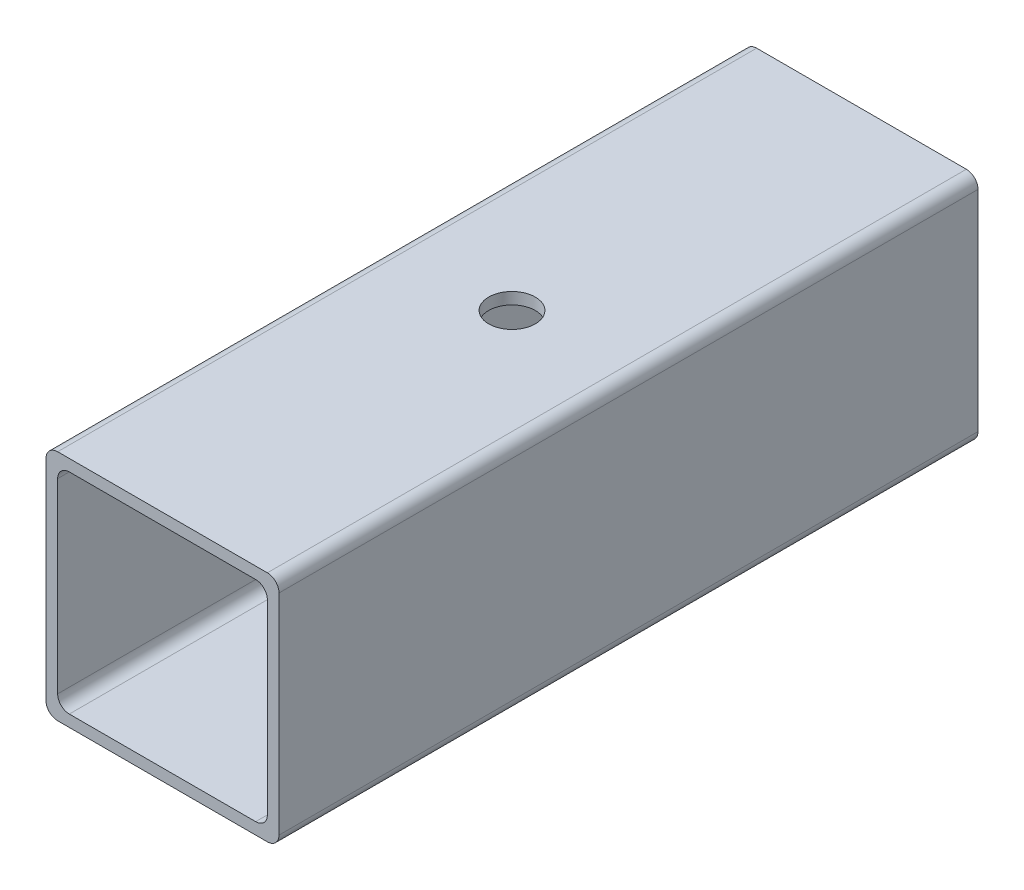
SolidWorks part; units mm, degrees
ref_plane "Płaszczyzna przednia" through (0, 0, 0) normal (0, 0, 1) x (1, 0, 0)
ref_plane "Płaszczyzna górna" through (0, 0, 0) normal (0, 1, 0) x (1, 0, 0)
ref_plane "Płaszczyzna prawa" through (0, 0, 0) normal (1, 0, 0) x (0, 0, -1)
sketch "Sketch1" plane through (0, 0, 0) normal (0, 0, 1) x (1, 0, 0)
  line L1 (-30, 30) -> (30, 30)
  line L2 (-30, 30) -> (-30, -30)
  line L3 (-30, -30) -> (30, -30)
  line L4 (30, 30) -> (30, -30)
  line L5 (-30, 30) -> (30, -30) construction
  line L6 (-30, -30) -> (30, 30) construction
  line L7 (-27, 27) -> (27, 27)
  line L8 (-27, 27) -> (-27, -27)
  line L9 (-27, -27) -> (27, -27)
  line L10 (27, 27) -> (27, -27)
  line L11 (-27, 27) -> (27, -27) construction
  line L12 (-27, -27) -> (27, 27) construction
  point P0 (0, 0)
  point P6 (0, 0)
  dimension "D1" = 60
  dimension "D2" = 60
  dimension "D3" = 54
  dimension "D4" = 54
extrude "Boss-Extrude1" add sketch "Sketch1" along normal blind 180
fillet "Fillet1" radius 3 8 edges at (-27, -27, 90) (27, -27, 90) (27, 27, 90) (-27, 27, 90) (30, -30, 90) (-30, -30, 90) (-30, 30, 90) (30, 30, 90)
sketch "Sketch2" plane through (0, 0, 0) normal (0, 1, 0) x (1, 0, 0)
  line L0 (0, 0) -> (0, -180) construction
  line L1 (27, -180) -> (-27, -180) construction
  line L2 (-30, -90) -> (30, -90) construction
  line L3 (-30, -180) -> (-30, 0) construction
  line L4 (30, 0) -> (30, -180) construction
  circle A0 centre (0, -90) radius 6
  dimension "D1" = 12
extrude "Cut-Extrude1" cut sketch "Sketch2" against normal through all both and the other way through all
